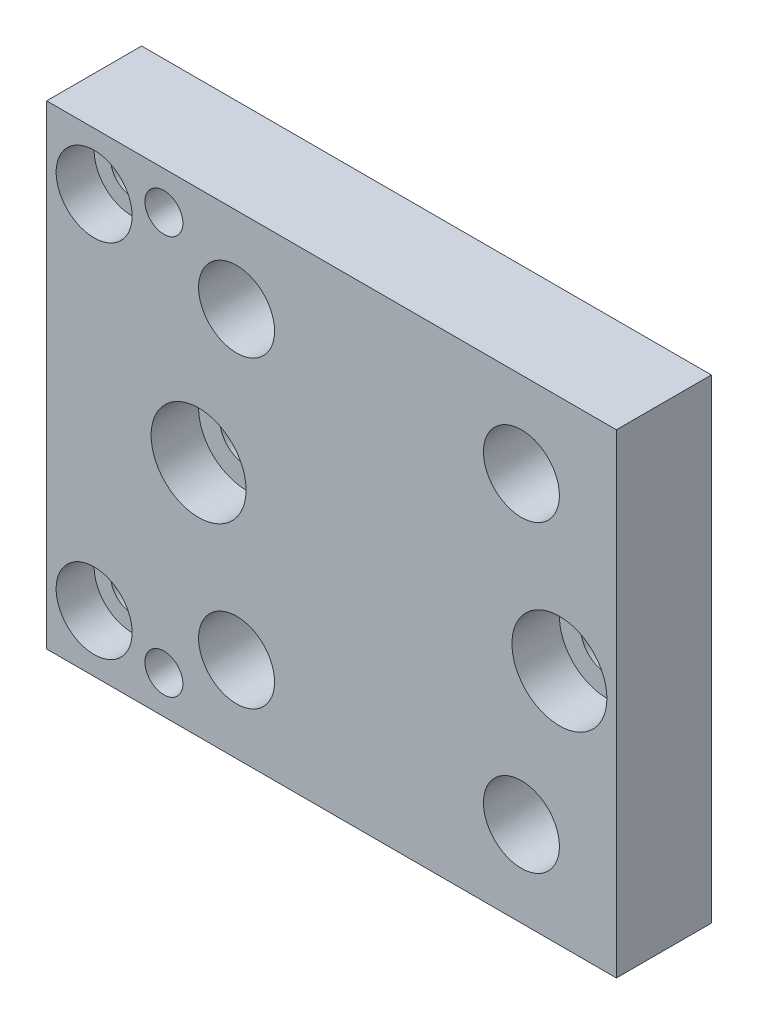
SolidWorks part; units mm, degrees
ref_plane "Front Plane" through (0, 0, 0) normal (0, 0, 1) x (1, 0, 0)
ref_plane "Top Plane" through (0, 0, 0) normal (0, 1, 0) x (1, 0, 0)
ref_plane "Right Plane" through (0, 0, 0) normal (1, 0, 0) x (0, 0, -1)
sketch "Sketch1" plane through (0, 0, 0) normal (0, 0, 1) x (1, 0, 0)
  line L1 (0, 0) -> (-60, 0)
  line L2 (0, 0) -> (0, 50)
  line L3 (0, 50) -> (-60, 50)
  line L4 (-60, 0) -> (-60, 50)
  circle A0 centre (-10, 41) radius 4
  circle A1 centre (-10, 9) radius 4
  circle A2 centre (-40, 9) radius 4
  circle A3 centre (-40, 41) radius 4
  circle A4 centre (-55, 44) radius 2.25
  circle A5 centre (-55, 6) radius 2.25
  circle A6 centre (-44, 25) radius 2.75
  circle A7 centre (-6, 25) radius 2.75
  circle A8 centre (-47.6525, 46) radius 2
  circle A9 centre (-47.6525, 4) radius 2
  point P25 (0, 0)
  point P26 (0, 0)
  point P27 (0, 0)
  point P28 (0, 0)
  point P29 (0, 0)
  point P30 (0, 0)
  point P31 (0, 0)
  dimension "D3" = 4.5
  dimension "D4" = 5
  dimension "D5" = 6
  dimension "D6" = 44
  dimension "D7" = 4
  dimension "D8" = 4
  dimension "D9" = 46
  dimension "D10" = 8
  dimension "D11" = 10
  dimension "D12" = 9
  dimension "D13" = 41
  dimension "D14" = 40
  dimension "D15" = 5.5
  dimension "D16" = 44
  dimension "D17" = 6
  dimension "D18" = 25
  dimension "D1" = 60
  dimension "D2" = 50
extrude "Boss-Extrude2" add sketch "Sketch1" along normal blind 10
sketch "Sketch2" plane through (0, 0, 10) normal (0, 0, 1) x (1, 0, 0)
  circle A0 centre (-55, 44) radius 4
  circle A1 centre (-55, 6) radius 4
  dimension "D1" = 8
  dimension "D2" = 8
extrude "Cut-Extrude1" cut sketch "Sketch2" against normal blind 4
sketch "Sketch3" plane through (0, 0, 10) normal (0, 0, 1) x (1, 0, 0)
  circle A0 centre (-44, 25) radius 5
  circle A1 centre (-6, 25) radius 5
  dimension "D1" = 10
  dimension "D2" = 10
extrude "Cut-Extrude2" cut sketch "Sketch3" against normal blind 5
